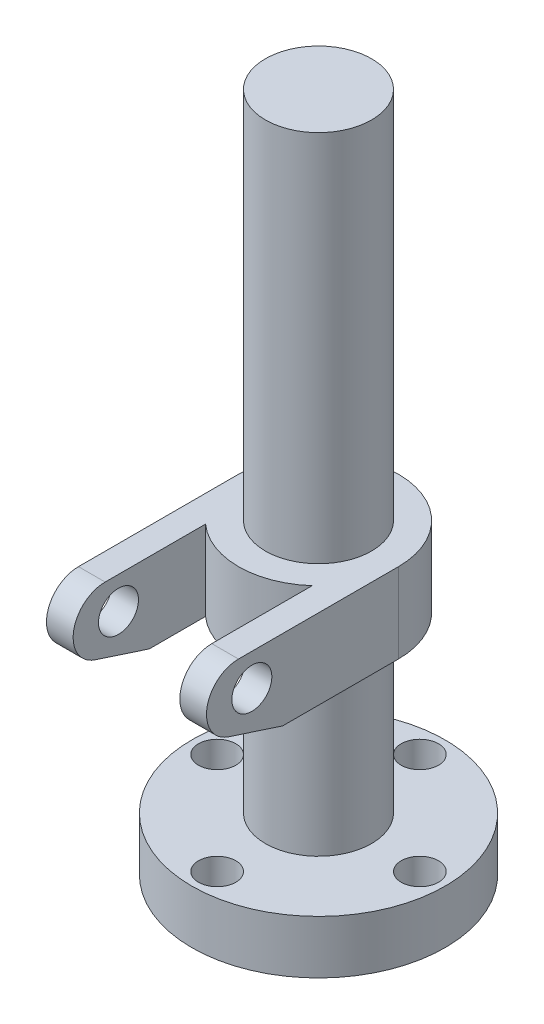
SolidWorks part; units mm, degrees
material "Ti-6Al-4VSolution treated and aged (SS)"
ref_plane "Front Plane" through (0, 0, 0) normal (0, 0, 1) x (1, 0, 0)
ref_plane "Top Plane" through (0, 0, 0) normal (0, 1, 0) x (1, 0, 0)
ref_plane "Right Plane" through (0, 0, 0) normal (1, 0, 0) x (0, 0, -1)
sketch "Sketch1" plane through (0, 0, 0) normal (0, 0, 1) x (1, 0, 0)
  line L0 (0, 307.0262) -> (0, -293.8835) construction
  line L1 (-225.6352, 0) -> (258.5932, 0) construction
  line L2 (0, 0) -> (47.5, 0)
  line L3 (47.5, 0) -> (47.5, 20)
  line L4 (47.5, 20) -> (19.9, 20)
  line L5 (19.9, 20) -> (19.9, 85)
  line L6 (19.9, 85) -> (30, 85)
  line L7 (30, 85) -> (30, 115)
  line L8 (30, 115) -> (19.9, 115)
  line L9 (19.9, 115) -> (19.9, 255)
  line L10 (19.9, 255) -> (0, 255)
  line L11 (0, 255) -> (0, 0)
  dimension "D1" = 20
  dimension "D2" = 65
  dimension "D3" = 30
  dimension "D4" = 140
  dimension "D5" = 47.5
  dimension "D6" = 19.9
  dimension "D7" = 19.9
  dimension "D8" = 30
revolve "Revolve1" add sketch "Sketch1" angle 360 about L0
ref_plane "Plane1" through (0, 85, 0) normal (0, 1, 0) x (1, 0, 0)
sketch "Sketch2" plane through (0, 85, 0) normal (0, 1, 0) x (1, 0, 0)
  line L0 (0, 43.5167) -> (0, -92.2099) construction
  line L1 (-75.2233, 0) -> (124.2039, 0) construction
  line L2 (-30, 0) -> (-30, -80)
  line L3 (-30, -80) -> (-20, -80)
  line L4 (-20, -80) -> (-20, 0)
  line L5 (-20, 0) -> (-30, 0)
  line L6 (30, -80) -> (20, -80)
  line L7 (20, 0) -> (30, 0)
  line L8 (20, -80) -> (20, 0)
  line L9 (30, 0) -> (30, -80)
  circle A0 centre (0, 0) radius 30 construction
  dimension "D1" = 10
  dimension "D2" = 80
extrude "Boss-Extrude1" add sketch "Sketch2" along normal up to surface (30 mm away) up to face at (0, 115, 19.9)
sketch "Sketch3" plane through (-30, 0, 0) normal (-1, 0, 0) x (0, 0, 1)
  line L0 (80, 115) -> (0, 115) construction
  line L1 (0, 115) -> (0, 85) construction
  line L2 (43.4422, 85) -> (63.7095, 91.5877)
  line L3 (60, 115) -> (80, 115)
  line L4 (80, 115) -> (80, 85)
  line L5 (80, 85) -> (43.4422, 85)
  line L6 (0, 85) -> (80, 85) construction
  circle A0 centre (55, 103) radius 7.5
  arc A1 (63.7095, 91.5877) -> (60, 115) centre (60, 103) ccw
  dimension "D1" = 12
  dimension "D3" = 15
  dimension "D5" = 24
  dimension "D2" = 55
  dimension "D4" = 60
extrude "Cut-Extrude1" cut sketch "Sketch3" against normal blind 94
sketch "Sketch4" plane through (0, 20, 0) normal (0, 1, 0) x (1, 0, 0)
  line L0 (0, 61.3903) -> (0, -79.676) construction
  line L1 (-73.4406, 0) -> (57.7187, 0) construction
  circle A0 centre (0, 0) radius 38 construction
  dimension "D1" = 76
hole_wizard "Hole1" positions "Sketch5" profile "Sketch6" legacy end condition through all
sketch "Sketch5" plane through (0, 20, 0) normal (0, 1, 0) x (1, 0, 0)
  line L0 (-73.4406, 0) -> (57.7187, 0) construction
  line L1 (0, 61.3903) -> (0, -79.676) construction
  circle A0 centre (0, 0) radius 38 construction
  point P0 (38, 0)
  point P6 (0, 38)
  point P10 (-38, 0)
  point P12 (0, -38)
sketch "Sketch6" plane through (38, 20, 0) normal (1, 0, 0) x (0, 0, 1)
  line L0 (0, 0) -> (0, 20)
  line L1 (0, 20) -> (5, 20)
  line L2 (5, 20) -> (5, 10)
  line L3 (5, 10) -> (7, 10)
  line L4 (7, 10) -> (7, 0)
  line L5 (7, 0) -> (0, 0)
  line L6 (0, 110) -> (0, -10) construction
  dimension "Diameter" = 10
  dimension "Depth" = 20
  dimension "C-Bore Diameter" = 14
  dimension "C-Bore Depth" = 10
sketch "Sketch8" plane through (0, 0, 0) normal (0, -1, 0) x (1, 0, 0)
  circle A0 centre (0, 0) radius 20
  dimension "D1" = 40
extrude "Cut-Extrude2" cut sketch "Sketch8" against normal blind 15
